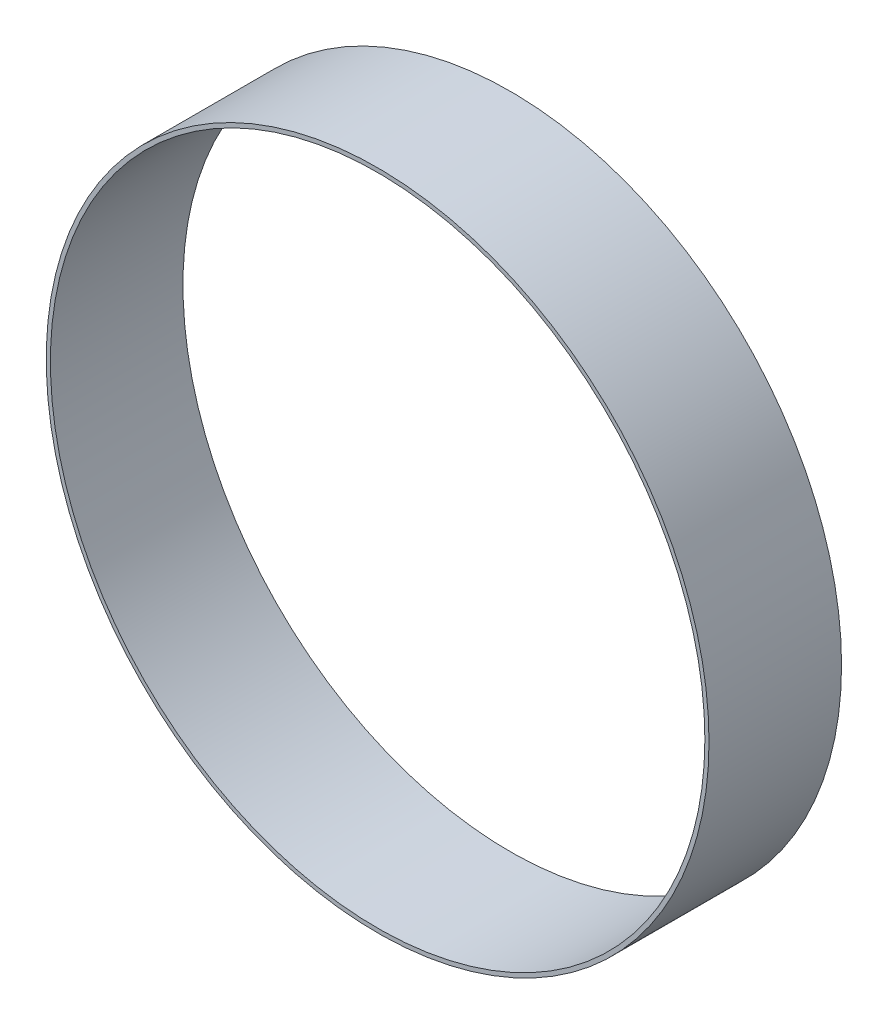
SolidWorks part; units mm, degrees
material "Plain Carbon Steel"
ref_plane "Front Plane" through (0, 0, 0) normal (0, 0, 1) x (1, 0, 0)
ref_plane "Top Plane" through (0, 0, 0) normal (0, 1, 0) x (1, 0, 0)
ref_plane "Right Plane" through (0, 0, 0) normal (1, 0, 0) x (0, 0, -1)
sketch "Sketch1" plane through (0, 0, 0) normal (0, 0, 1) x (1, 0, 0)
  circle A0 centre (0, 0) radius 127
  dimension "D1" = 254
extrude "Boss-Extrude1" add sketch "Sketch1" along normal blind 50.8 contours A0
sketch "Sketch2" plane through (0, 0, 50.8) normal (0, 0, 1) x (1, 0, 0)
  circle A0 centre (0, 0) radius 125.4125
  dimension "D1" = 250.825
extrude "Cut-Extrude1" cut sketch "Sketch2" against normal blind 50.8
